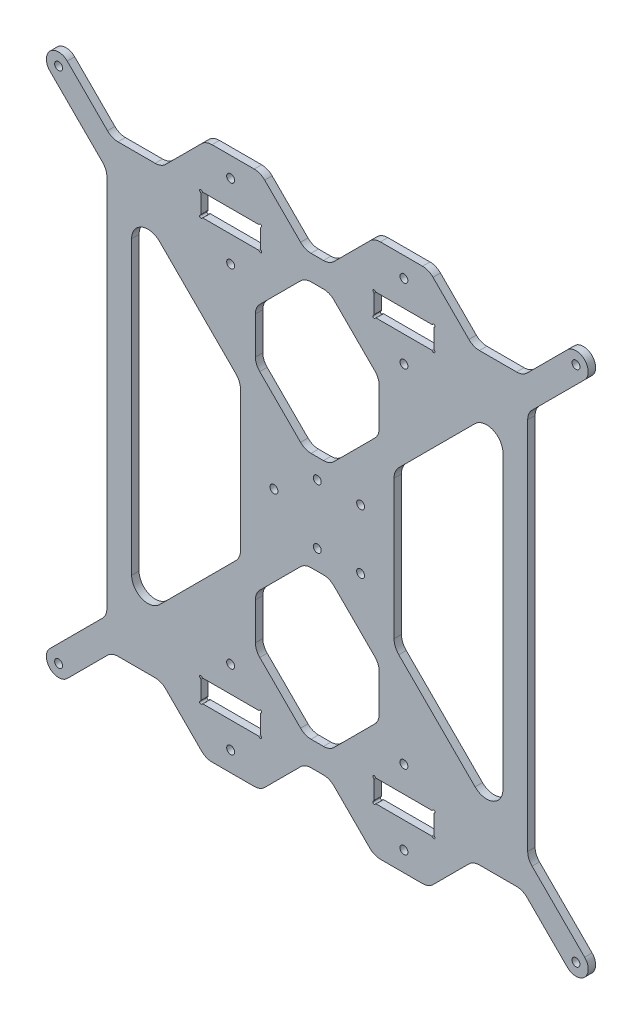
SolidWorks part; units mm, degrees
ref_plane "Alzado" through (0, 0, 0) normal (0, 0, 1) x (1, 0, 0)
ref_plane "Planta" through (0, 0, 0) normal (0, 1, 0) x (1, 0, 0)
ref_plane "Vista lateral" through (0, 0, 0) normal (1, 0, 0) x (0, 0, -1)
sketch "Model" plane through (0, 0, 0) normal (0, 0, 1) x (1, 0, 0)
  line L0 (91.8919, 29.1458) -> (77.4066, 43.631)
  line L1 (73.164, 45.3884) -> (58.1345, 45.3884)
  line L2 (53.8919, 43.631) -> (37.6493, 27.3884)
  line L3 (30.6493, 34.3884) -> (51.8919, 55.631)
  line L4 (53.6493, 59.8737) -> (53.6493, 210.9031)
  line L5 (51.8919, 215.1458) -> (30.6493, 236.3884)
  line L6 (37.6493, 243.3884) -> (53.8919, 227.1458)
  line L7 (223.4065, 227.1457) -> (239.6493, 243.3884)
  line L8 (246.6493, 236.3884) -> (225.4066, 215.1458)
  line L9 (223.6493, 210.9031) -> (223.6493, 150.3381)
  line L10 (225.4066, 55.631) -> (246.6493, 34.3884)
  line L11 (239.6493, 27.3884) -> (223.4066, 43.631)
  line L12 (219.164, 45.3884) -> (204.1345, 45.3884)
  line L13 (199.8919, 43.631) -> (185.4066, 29.1458)
  line L14 (181.164, 27.3884) -> (164.1345, 27.3884)
  line L15 (159.8919, 29.1458) -> (145.4066, 43.631)
  line L16 (141.164, 45.3884) -> (136.1345, 45.3884)
  line L17 (131.8919, 43.631) -> (117.4066, 29.1458)
  line L18 (113.164, 27.3884) -> (96.1345, 27.3884)
  line L19 (171.5824, 168.1215) -> (202.3824, 198.9215)
  line L20 (213.6493, 194.2546) -> (213.6493, 76.5222)
  line L21 (202.3824, 71.8553) -> (171.5824, 102.6553)
  line L22 (169.6493, 107.3222) -> (169.6493, 163.4546)
  line L23 (131.8919, 57.1458) -> (115.4066, 73.631)
  line L24 (113.6493, 77.8737) -> (113.6493, 92.9031)
  line L25 (115.4066, 97.1458) -> (131.8919, 113.631)
  line L26 (136.1345, 115.3884) -> (141.164, 115.3884)
  line L27 (145.4066, 113.631) -> (161.8919, 97.1458)
  line L28 (163.6493, 92.9031) -> (163.6493, 77.8737)
  line L29 (161.8919, 73.631) -> (145.4066, 57.1458)
  line L30 (141.164, 55.3884) -> (136.1345, 55.3884)
  line L31 (161.8919, 173.631) -> (145.4066, 157.1458)
  line L32 (141.164, 155.3884) -> (136.1345, 155.3884)
  line L33 (131.8919, 157.1458) -> (115.4066, 173.631)
  line L34 (185.6993, 46.7544) -> (185.6993, 54.0223)
  line L35 (92.4653, 45.8883) -> (114.8332, 45.8883)
  line L36 (115.6992, 46.7544) -> (115.6992, 54.0223)
  line L37 (114.8332, 54.8883) -> (92.4653, 54.8883)
  line L38 (91.5992, 54.0223) -> (91.5992, 46.7544)
  line L39 (162.4653, 45.8883) -> (184.8332, 45.8883)
  line L40 (184.8332, 54.8884) -> (162.4653, 54.8884)
  line L41 (161.5993, 54.0223) -> (161.5993, 46.7544)
  line L42 (107.6493, 163.4546) -> (107.6493, 107.3222)
  line L43 (105.7162, 102.6553) -> (74.9162, 71.8553)
  line L44 (74.9162, 198.9215) -> (105.7162, 168.1215)
  line L45 (63.6493, 76.5222) -> (63.6493, 194.2546)
  line L46 (91.892, 241.6311) -> (77.4067, 227.1458)
  line L47 (199.8919, 227.1457) -> (185.4067, 241.631)
  line L48 (181.164, 243.3883) -> (164.1346, 243.3884)
  line L49 (159.892, 241.631) -> (145.4067, 227.1457)
  line L50 (141.164, 225.3884) -> (136.1346, 225.3884)
  line L51 (131.8919, 227.1457) -> (117.4067, 241.631)
  line L52 (113.164, 243.3884) -> (96.1346, 243.3884)
  line L53 (141.164, 215.3884) -> (136.1346, 215.3884)
  line L54 (185.6993, 224.0223) -> (185.6993, 216.7543)
  line L55 (92.4653, 224.8884) -> (114.8333, 224.8884)
  line L56 (115.6993, 224.0223) -> (115.6993, 216.7544)
  line L57 (114.8332, 215.8884) -> (92.4653, 215.8884)
  line L58 (91.5993, 216.7544) -> (91.5993, 224.0224)
  line L59 (162.4653, 224.8883) -> (184.8333, 224.8883)
  line L60 (184.8333, 215.8883) -> (162.4653, 215.8883)
  line L61 (161.5993, 216.7543) -> (161.5993, 224.0223)
  line L62 (131.8919, 213.631) -> (115.4066, 197.1457)
  line L63 (161.8919, 197.1457) -> (145.4067, 213.631)
  line L64 (113.6493, 192.9031) -> (113.6493, 177.8737)
  line L65 (163.6493, 177.8736) -> (163.6493, 192.9031)
  line L66 (73.164, 225.3884) -> (58.1345, 225.3884)
  line L67 (219.1639, 225.3883) -> (204.1346, 225.3883)
  line L68 (223.6493, 59.8737) -> (223.6493, 120.4387)
  line L69 (223.6493, 150.3381) -> (223.6493, 120.4387)
  arc A0 (77.4066, 43.631) -> (73.164, 45.3884) centre (73.164, 39.3884) ccw
  arc A1 (58.1345, 45.3884) -> (53.8919, 43.631) centre (58.1345, 39.3884) ccw
  arc A2 (30.6493, 34.3884) -> (37.6493, 27.3884) centre (34.1493, 30.8884) ccw
  arc A3 (51.8919, 55.631) -> (53.6493, 59.8737) centre (47.6493, 59.8737) ccw
  arc A4 (53.6493, 210.9031) -> (51.8919, 215.1458) centre (47.6493, 210.9031) ccw
  arc A5 (37.6493, 243.3884) -> (30.6493, 236.3884) centre (34.1493, 239.8884) ccw
  arc A6 (246.6493, 236.3884) -> (239.6493, 243.3884) centre (243.1493, 239.8884) ccw
  arc A7 (225.4066, 215.1458) -> (223.6493, 210.9031) centre (229.6493, 210.9031) ccw
  arc A8 (223.6493, 59.8737) -> (225.4066, 55.631) centre (229.6493, 59.8737) ccw
  arc A9 (239.6493, 27.3884) -> (246.6493, 34.3884) centre (243.1493, 30.8884) ccw
  arc A10 (223.4066, 43.631) -> (219.164, 45.3884) centre (219.164, 39.3884) ccw
  arc A11 (204.1345, 45.3884) -> (199.8919, 43.631) centre (204.1345, 39.3884) ccw
  arc A12 (181.164, 27.3884) -> (185.4066, 29.1458) centre (181.164, 33.3884) ccw
  arc A13 (159.8919, 29.1458) -> (164.1345, 27.3884) centre (164.1345, 33.3884) ccw
  arc A14 (145.4066, 43.631) -> (141.164, 45.3884) centre (141.164, 39.3884) ccw
  arc A15 (136.1345, 45.3884) -> (131.8919, 43.631) centre (136.1345, 39.3884) ccw
  arc A16 (113.164, 27.3884) -> (117.4066, 29.1458) centre (113.164, 33.3884) ccw
  arc A17 (91.8919, 29.1458) -> (96.1345, 27.3884) centre (96.1345, 33.3884) ccw
  arc A18 (213.6493, 194.2546) -> (202.3824, 198.9215) centre (207.0493, 194.2546) ccw
  arc A19 (202.3824, 71.8553) -> (213.6493, 76.5222) centre (207.0493, 76.5222) ccw
  arc A20 (169.6493, 107.3222) -> (171.5824, 102.6553) centre (176.2493, 107.3222) ccw
  arc A21 (171.5824, 168.1215) -> (169.6493, 163.4546) centre (176.2493, 163.4546) ccw
  arc A22 (113.6493, 77.8737) -> (115.4066, 73.631) centre (119.6493, 77.8737) ccw
  arc A23 (115.4066, 97.1458) -> (113.6493, 92.9031) centre (119.6493, 92.9031) ccw
  arc A24 (136.1345, 115.3884) -> (131.8919, 113.631) centre (136.1345, 109.3884) ccw
  arc A25 (145.4066, 113.631) -> (141.164, 115.3884) centre (141.164, 109.3884) ccw
  arc A26 (163.6493, 92.9031) -> (161.8919, 97.1458) centre (157.6493, 92.9031) ccw
  arc A27 (161.8919, 73.631) -> (163.6493, 77.8737) centre (157.6493, 77.8737) ccw
  arc A28 (141.164, 55.3884) -> (145.4066, 57.1458) centre (141.164, 61.3884) ccw
  arc A29 (131.8919, 57.1458) -> (136.1345, 55.3884) centre (136.1345, 61.3884) ccw
  arc A30 (141.164, 155.3884) -> (145.4066, 157.1458) centre (141.164, 161.3884) ccw
  arc A31 (131.8919, 157.1458) -> (136.1345, 155.3884) centre (136.1345, 161.3884) ccw
  arc A32 (113.6493, 177.8737) -> (115.4066, 173.631) centre (119.6493, 177.8737) ccw
  arc A33 (161.8919, 173.631) -> (163.6493, 177.8736) centre (157.6493, 177.8737) ccw
  arc A34 (115.2662, 45.6383) -> (114.8332, 45.8883) centre (114.8332, 45.3883) ccw
  arc A35 (115.2662, 45.6383) -> (115.9492, 46.3213) centre (115.6992, 45.8883) ccw
  arc A36 (115.6992, 46.7544) -> (115.9492, 46.3213) centre (116.1992, 46.7544) ccw
  arc A37 (115.9492, 54.4553) -> (115.6992, 54.0223) centre (116.1992, 54.0223) ccw
  arc A38 (115.9492, 54.4553) -> (115.2662, 55.1383) centre (115.6992, 54.8883) ccw
  arc A39 (114.8332, 54.8883) -> (115.2662, 55.1383) centre (114.8332, 55.3883) ccw
  arc A40 (92.0323, 55.1383) -> (92.4653, 54.8883) centre (92.4653, 55.3883) ccw
  arc A41 (92.0323, 55.1383) -> (91.3492, 54.4553) centre (91.5992, 54.8883) ccw
  arc A42 (91.5992, 54.0223) -> (91.3492, 54.4553) centre (91.0992, 54.0223) ccw
  arc A43 (91.3492, 46.3213) -> (91.5992, 46.7544) centre (91.0992, 46.7544) ccw
  arc A44 (91.3492, 46.3213) -> (92.0323, 45.6383) centre (91.5992, 45.8883) ccw
  arc A45 (92.4653, 45.8883) -> (92.0323, 45.6383) centre (92.4653, 45.3883) ccw
  circle A46 centre (243.1493, 30.8884) radius 1.6
  circle A47 centre (34.1493, 30.8884) radius 1.6
  circle A48 centre (173.6493, 35.3884) radius 1.6
  circle A49 centre (103.6493, 35.3884) radius 1.6
  circle A50 centre (173.6493, 65.3884) radius 1.6
  circle A51 centre (103.6493, 65.3884) radius 1.6
  circle A52 centre (156.1493, 123.3884) radius 1.6
  circle A53 centre (121.1493, 135.3884) radius 1.6
  circle A54 centre (156.1493, 147.3884) radius 1.6
  circle A55 centre (243.1493, 239.8884) radius 1.6
  circle A56 centre (34.1493, 239.8884) radius 1.6
  arc A57 (185.2663, 45.6383) -> (184.8332, 45.8883) centre (184.8332, 45.3883) ccw
  arc A58 (185.2663, 45.6383) -> (185.9493, 46.3214) centre (185.6993, 45.8884) ccw
  arc A59 (185.6993, 46.7544) -> (185.9493, 46.3214) centre (186.1993, 46.7544) ccw
  arc A60 (185.9493, 54.4553) -> (185.6993, 54.0223) centre (186.1993, 54.0223) ccw
  arc A61 (185.9493, 54.4553) -> (185.2663, 55.1384) centre (185.6993, 54.8884) ccw
  arc A62 (184.8332, 54.8884) -> (185.2663, 55.1384) centre (184.8332, 55.3884) ccw
  arc A63 (162.0323, 55.1384) -> (162.4653, 54.8884) centre (162.4653, 55.3884) ccw
  arc A64 (162.0323, 55.1384) -> (161.3493, 54.4553) centre (161.5993, 54.8884) ccw
  arc A65 (161.5993, 54.0223) -> (161.3493, 54.4553) centre (161.0993, 54.0223) ccw
  arc A66 (161.3493, 46.3214) -> (161.5993, 46.7544) centre (161.0993, 46.7544) ccw
  arc A67 (161.3493, 46.3214) -> (162.0323, 45.6383) centre (161.5993, 45.8884) ccw
  arc A68 (162.4653, 45.8883) -> (162.0323, 45.6383) centre (162.4653, 45.3883) ccw
  circle A69 centre (138.6493, 123.3884) radius 1.6
  circle A70 centre (138.6493, 147.3884) radius 1.6
  arc A71 (107.6493, 163.4546) -> (105.7162, 168.1215) centre (101.0493, 163.4546) ccw
  arc A72 (105.7162, 102.6553) -> (107.6493, 107.3222) centre (101.0493, 107.3222) ccw
  arc A73 (74.9162, 198.9215) -> (63.6493, 194.2546) centre (70.2493, 194.2546) ccw
  arc A74 (63.6493, 76.5222) -> (74.9162, 71.8553) centre (70.2492, 76.5222) ccw
  arc A75 (73.164, 225.3884) -> (77.4067, 227.1458) centre (73.164, 231.3884) ccw
  arc A76 (199.8919, 227.1457) -> (204.1346, 225.3883) centre (204.1346, 231.3883) ccw
  arc A77 (185.4067, 241.631) -> (181.164, 243.3883) centre (181.164, 237.3883) ccw
  arc A78 (164.1346, 243.3884) -> (159.892, 241.631) centre (164.1346, 237.3883) ccw
  arc A79 (141.164, 225.3884) -> (145.4067, 227.1457) centre (141.164, 231.3884) ccw
  arc A80 (131.8919, 227.1457) -> (136.1346, 225.3884) centre (136.1346, 231.3884) ccw
  arc A81 (117.4067, 241.631) -> (113.164, 243.3884) centre (113.164, 237.3884) ccw
  arc A82 (96.1346, 243.3884) -> (91.892, 241.6311) centre (96.1346, 237.3884) ccw
  arc A83 (145.4067, 213.631) -> (141.164, 215.3884) centre (141.164, 209.3884) ccw
  arc A84 (136.1346, 215.3884) -> (131.8919, 213.631) centre (136.1346, 209.3884) ccw
  arc A85 (114.8333, 224.8884) -> (115.2663, 225.1384) centre (114.8333, 225.3884) ccw
  arc A86 (115.9493, 224.4553) -> (115.2663, 225.1384) centre (115.6993, 224.8884) ccw
  arc A87 (115.9493, 224.4553) -> (115.6993, 224.0223) centre (116.1993, 224.0223) ccw
  arc A88 (115.6993, 216.7544) -> (115.9493, 216.3214) centre (116.1993, 216.7544) ccw
  arc A89 (115.2663, 215.6383) -> (115.9493, 216.3214) centre (115.6993, 215.8883) ccw
  arc A90 (115.2663, 215.6383) -> (114.8332, 215.8884) centre (114.8332, 215.3884) ccw
  arc A91 (92.4653, 215.8884) -> (92.0323, 215.6384) centre (92.4653, 215.3884) ccw
  arc A92 (91.3493, 216.3214) -> (92.0323, 215.6384) centre (91.5993, 215.8884) ccw
  arc A93 (91.3493, 216.3214) -> (91.5993, 216.7544) centre (91.0993, 216.7544) ccw
  arc A94 (91.5993, 224.0224) -> (91.3493, 224.4554) centre (91.0993, 224.0224) ccw
  arc A95 (92.0323, 225.1384) -> (91.3493, 224.4554) centre (91.5993, 224.8884) ccw
  arc A96 (92.0323, 225.1384) -> (92.4653, 224.8884) centre (92.4653, 225.3884) ccw
  circle A97 centre (173.6493, 235.3883) radius 1.6
  circle A98 centre (103.6493, 235.3884) radius 1.6
  arc A99 (184.8333, 224.8883) -> (185.2663, 225.1383) centre (184.8333, 225.3883) ccw
  arc A100 (185.9493, 224.4553) -> (185.2663, 225.1383) centre (185.6993, 224.8883) ccw
  arc A101 (185.9493, 224.4553) -> (185.6993, 224.0223) centre (186.1993, 224.0223) ccw
  arc A102 (185.6993, 216.7543) -> (185.9493, 216.3213) centre (186.1993, 216.7543) ccw
  arc A103 (185.2663, 215.6383) -> (185.9493, 216.3213) centre (185.6993, 215.8883) ccw
  arc A104 (185.2663, 215.6383) -> (184.8333, 215.8883) centre (184.8333, 215.3883) ccw
  arc A105 (162.4653, 215.8883) -> (162.0323, 215.6383) centre (162.4653, 215.3883) ccw
  arc A106 (161.3493, 216.3213) -> (162.0323, 215.6383) centre (161.5993, 215.8883) ccw
  arc A107 (161.3493, 216.3213) -> (161.5993, 216.7543) centre (161.0993, 216.7543) ccw
  arc A108 (161.5993, 224.0223) -> (161.3493, 224.4553) centre (161.0993, 224.0223) ccw
  arc A109 (162.0323, 225.1383) -> (161.3493, 224.4553) centre (161.5993, 224.8883) ccw
  arc A110 (162.0323, 225.1383) -> (162.4653, 224.8883) centre (162.4653, 225.3883) ccw
  arc A111 (115.4066, 197.1457) -> (113.6493, 192.9031) centre (119.6493, 192.9031) ccw
  arc A112 (163.6493, 192.9031) -> (161.8919, 197.1457) centre (157.6493, 192.9031) ccw
  circle A113 centre (173.6493, 205.3883) radius 1.6
  circle A114 centre (103.6493, 205.3884) radius 1.6
  arc A115 (219.1639, 225.3883) -> (223.4065, 227.1457) centre (219.1639, 231.3883) ccw
  arc A116 (53.8919, 227.1458) -> (58.1345, 225.3884) centre (58.1345, 231.3884) ccw
extrude "Saliente-Extruir1" add sketch "Model" along normal blind 3
